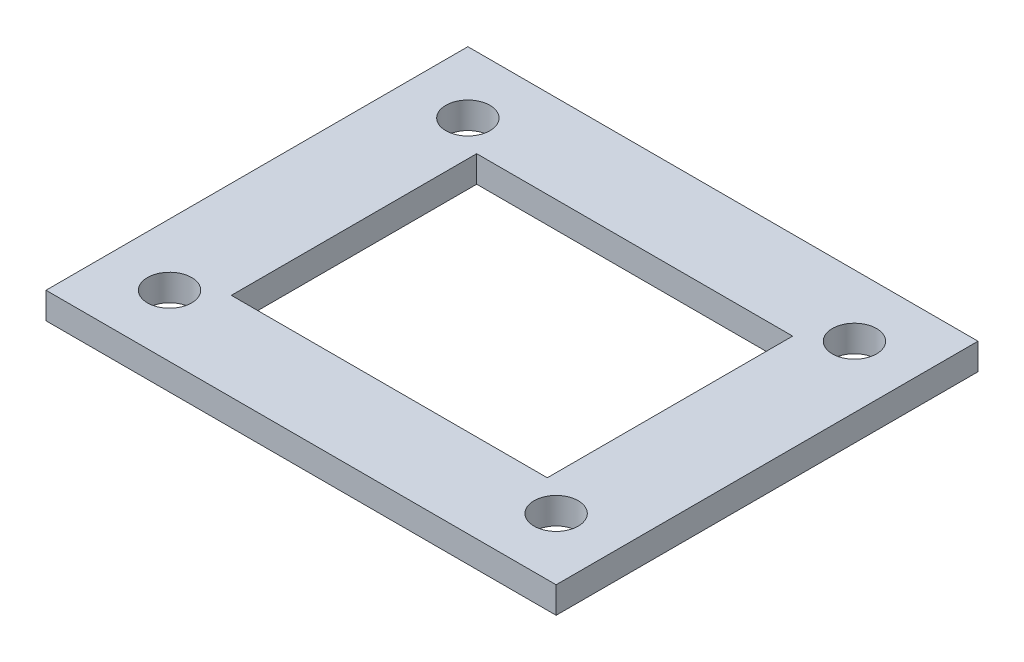
SolidWorks part; units mm, degrees
ref_plane "Front Plane" through (0, 0, 0) normal (0, 0, 1) x (1, 0, 0)
ref_plane "Top Plane" through (0, 0, 0) normal (0, 1, 0) x (1, 0, 0)
ref_plane "Right Plane" through (0, 0, 0) normal (1, 0, 0) x (0, 0, -1)
sketch "Sketch1" plane through (0, 0, 0) normal (0, 1, 0) x (1, 0, 0)
  line L1 (-24.9, -19.9) -> (24.9, -19.9)
  line L2 (-24.9, -19.9) -> (-24.9, 19.9)
  line L3 (-24.9, 19.9) -> (24.9, 19.9)
  line L4 (24.9, -19.9) -> (24.9, 19.9)
  line L5 (-24.9, -19.9) -> (24.9, 19.9) construction
  line L6 (-24.9, 19.9) -> (24.9, -19.9) construction
  point P0 (0, 0)
  dimension "D1" = 49.8
  dimension "D2" = 39.8
extrude "Boss-Extrude1" add sketch "Sketch1" along normal blind 3
sketch "Sketch2" plane through (0, 3, 0) normal (0, 1, 0) x (1, 0, 0)
  line L0 (21.9, 16.9) -> (-21.9, 16.9)
  line L1 (-21.9, 16.9) -> (-21.9, -16.9)
  line L2 (-21.9, -16.9) -> (21.9, -16.9)
  line L3 (21.9, -16.9) -> (21.9, 16.9)
  line L4 (24.9, -19.9) -> (24.9, 19.9)
  line L5 (24.9, 19.9) -> (-24.9, 19.9)
  line L6 (-24.9, 19.9) -> (-24.9, -19.9)
  line L7 (-24.9, -19.9) -> (24.9, -19.9)
  line L8 (24.9, -19.9) -> (24.9, 19.9)
  line L9 (24.9, 19.9) -> (-24.9, 19.9)
  line L10 (-24.9, 19.9) -> (-24.9, -19.9)
  line L11 (-24.9, -19.9) -> (24.9, -19.9)
  circle A0 centre (-21.9, 16.9) radius 2.5
  dimension "D3" = 5
  dimension "D1" = 0
  dimension "D2" = 3
extrude "Cut-Extrude1" cut sketch "Sketch2" against normal blind 3 contours L0 A0 L1 | L1 A0 L0
ref_plane "Plane1" through (0, 0, 0) normal (1, 0, 0) x (0, 0, -1)
ref_plane "Plane2" through (0, 0, 0) normal (0, 0, -1) x (-1, 0, 0)
mirror "Mirror1" about plane through (0, 0, 0) normal (1, 0, 0) of "Cut-Extrude1" second plane through (0, 0, 0) second plane normal (0, 0, -1)
sketch "Sketch3" plane through (0, 3, 0) normal (0, 1, 0) x (1, 0, 0)
  line L0 (24.9, -19.9) -> (24.9, 19.9) construction
  line L1 (-17.9, -13.9) -> (17.9, -13.9)
  line L2 (-17.9, -13.9) -> (-17.9, 13.9)
  line L3 (-17.9, 13.9) -> (17.9, 13.9)
  line L4 (17.9, -13.9) -> (17.9, 13.9)
  line L5 (-17.9, -13.9) -> (17.9, 13.9) construction
  line L6 (-17.9, 13.9) -> (17.9, -13.9) construction
  line L7 (24.9, 19.9) -> (-24.9, 19.9) construction
  point P0 (0, 0)
  dimension "D1" = 7
  dimension "D2" = 6
extrude "Cut-Extrude2" cut sketch "Sketch3" against normal blind 3
sketch "Sketch4" plane through (0, 3, 0) normal (0, 1, 0) x (1, 0, 0)
  line L5 (-24.9, -19.9) -> (24.9, -19.9)
  line L6 (-24.9, -19.9) -> (-24.9, 19.9)
  line L7 (-24.9, 19.9) -> (24.9, 19.9)
  line L8 (28.9, -23.9) -> (28.9, 23.9)
  line L9 (28.9, 23.9) -> (-28.9, 23.9)
  line L10 (-28.9, 23.9) -> (-28.9, -23.9)
  line L11 (-28.9, -23.9) -> (28.9, -23.9)
  line L12 (28.9, -23.9) -> (28.9, 23.9)
  line L13 (28.9, 23.9) -> (-28.9, 23.9)
  line L14 (-28.9, 23.9) -> (-28.9, -23.9)
  line L15 (-28.9, -23.9) -> (28.9, -23.9)
  line L16 (24.9, -19.9) -> (24.9, 19.9)
  line L17 (-24.9, -19.9) -> (24.9, 19.9) construction
  line L18 (-24.9, 19.9) -> (24.9, -19.9) construction
  point P0 (0, 0)
  dimension "D1" = 4
extrude "Boss-Extrude2" add sketch "Sketch4" against normal up to surface (3 mm away) up to face at (0, 0, 0)
